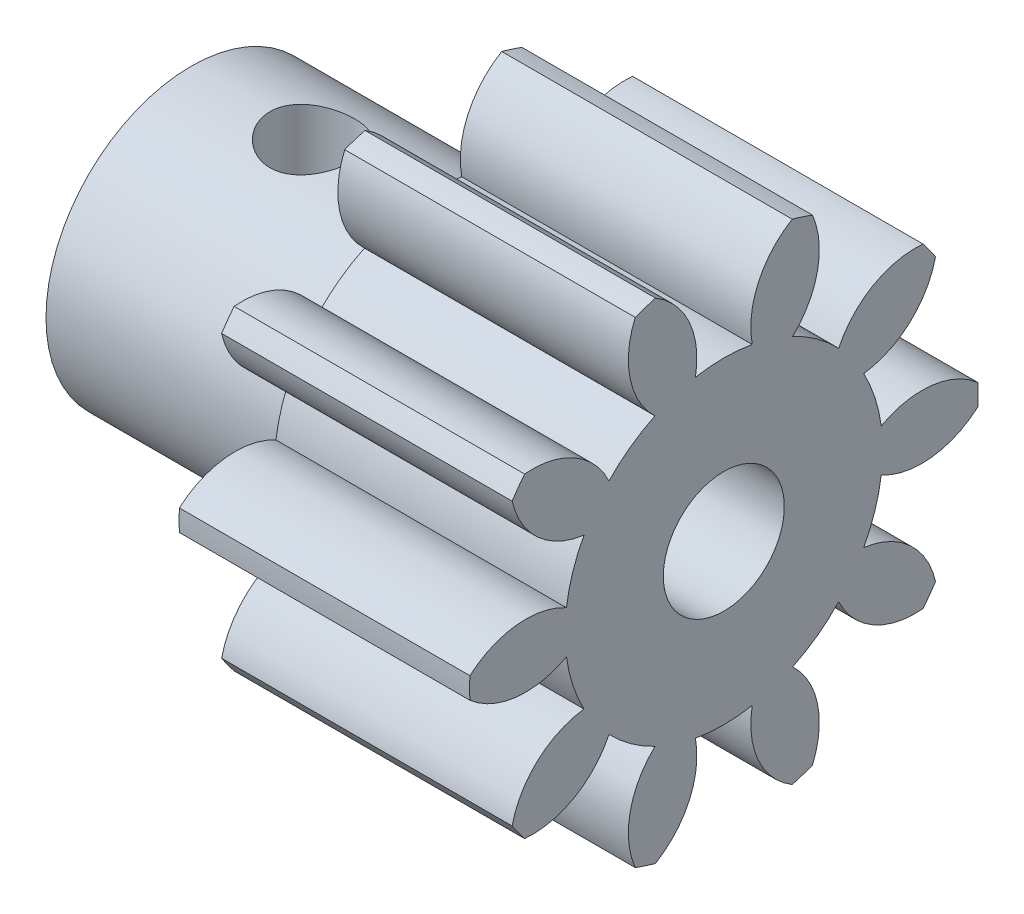
SolidWorks part; units mm, degrees
ref_plane "Plane1" through (0, 0, 0) normal (0, 0, 1) x (1, 0, 0)
ref_plane "Plane2" through (0, 0, 0) normal (0, 1, 0) x (1, 0, 0)
ref_plane "Plane3" through (0, 0, 0) normal (1, 0, 0) x (0, 0, -1)
sketch "HoldingSke" plane through (0, 0, 0) normal (0, 1, 0) x (1, 0, 0)
  line L0 (0, 0) -> (0.5627, -0.0992)
  line L1 (-15, 0) -> (100, 0) construction
  line L2 (0, 0) -> (-2.1039, 2.3779)
  line L3 (0, 0) -> (-11.863, 4.5341)
  line L4 (0, 0) -> (8.5048, 1.4996)
  line L5 (0, 0) -> (-46.8476, -17.4728)
  line L6 (0, 0) -> (-9.9476, -6.7116)
  line L7 (-2.1039, 2.3779) -> (8.6586, 51.2059)
  line L8 (-76.2, 54.61) -> (-75.3, 54.61)
  line L9 (-67.7845, 28.3722) -> (-49.3413, 33.142)
  line L10 (-76.2, 71.12) -> (104.1128, 71.12)
  line L11 (0, 0) -> (-12, 0)
  line L12 (-76.2, 101.6) -> (-76.147, 101.6)
  line L13 (24.9733, 27.94) -> (52.9518, 28.4284)
  line L14 (24.9733, 27.94) -> (24.9743, 27.94)
  line L15 (24.9733, 27.94) -> (100.4006, 29.5858)
  line L16 (-63.627, -1.75) -> (-12.827, -1.75)
  circle A0 centre (0, 0) radius 2.5
  circle A1 centre (0, 0) radius 6.5615
  circle A2 centre (0, 0) radius 37.5
  circle A3 centre (0, 0) radius 2.5
  dimension "MHD" = 13.123
  dimension "Hub_dia" = 75
  dimension "Bore" = 5
  dimension "MBD" = 5
  dimension "Num_teeth" = 10
  dimension "Pitch" = 0.5714
  dimension "Overall_len" = 50
  dimension "Show_teeth" = 10
  dimension "Thickness" = 12
  dimension "OAL" = 50.0001
  dimension "T_dim" = 0.9
  dimension "Ap" = 14.5
  dimension "H" = 19.05
  dimension "Pitch_radius" = 180.3128
  dimension "Width" = 12
  dimension "Backlash" = 0.053
  dimension "Addendum_fac" = 1
  dimension "Dedendum_fac" = 1.25
  dimension "Clearance_fac" = 0.25
  dimension "Dedendum_add" = 0.001
  dimension "Module" = 1.75
sketch "BasProSke" plane through (0, 0, 0) normal (0, 1, 0) x (1, 0, 0)
  line L0 (-10, 0) -> (60, 0) construction
  line L1 (0, 0) -> (0, 10.5)
  line L2 (0, 0) -> (12, 0)
  line L3 (12, 0) -> (12, 10.5)
  line L4 (12, 10.5) -> (0, 10.5)
  dimension "Thickness" = 12
  dimension "Diameter" = 21
revolve "Base-Revolve" add sketch "BasProSke" angle 360 about L0
sketch "TooCutSke" plane through (0, 0, 0) normal (1, 0, 0) x (0, 0, -1)
  line L1 (0, 0) -> (0, 107) construction
  line L2 (0, 0) -> (-1.4614, 8.6271) construction
  line L3 (0, 0) -> (-5.35, 16.4656) construction
  line L4 (-1.4614, 8.6271) -> (-2.675, 8.2328) construction
  arc A0 (1.1739, 6.4556) -> (-1.1739, 6.4556) centre (0, 0) ccw
  arc A1 (2.8542, 10.131) -> (-2.8542, 10.131) centre (0, 0) ccw
  circle A2 centre (0, 0) radius 8.75 construction
  circle A3 centre (0, 0) radius 8.4713 construction
  arc A4 (-1.1739, 6.4556) -> (-2.8542, 10.131) centre (-4.6131, 7.1051) ccw
  arc A5 (2.8542, 10.131) -> (1.1739, 6.4556) centre (4.6131, 7.1051) ccw
  dimension "Root_dia" = 13.123
  dimension "Overcut_dia" = 21.0508
  dimension "Pitch_dia" = 17.5
  dimension "Base_dia" = 16.9426
  dimension "Flank_rad" = 3.5
  dimension "Half_ang" = 18
  dimension "Half_CT" = 1.2761
extrude "ToothCut" cut sketch "TooCutSke" along normal through all
fillet "Breaks" [suppressed] radius 0.035
fillet "RootFillets" [suppressed] radius 0.4385
pattern_circular "TeethCuts" count 10 every 36 about axis through (-10, 0, 0) along (1, 0, 0) of "ToothCut"
sketch "HubNeaOneSke" plane through (0, 0, 0) normal (-1, 0, 0) x (0, 0, 1)
  circle A0 centre (0, 0) radius 6.5615
  dimension "Diameter" = 13.123
extrude "HubNearOne" [suppressed] add sketch "HubNeaOneSke" along normal blind 38.0001
sketch "HubNeaBotSke" plane through (0, 0, 0) normal (-1, 0, 0) x (0, 0, 1)
  circle A0 centre (0, 0) radius 6.5615
  dimension "Diameter" = 13.123
extrude "HubNearBoth" [suppressed] add sketch "HubNeaBotSke" along normal blind 19
ref_plane "FarPln" through (12, 0, 0) normal (1, 0, 0) x (0, 0, -1)
sketch "HubFarSke" plane through (12, 0, 0) normal (1, 0, 0) x (0, 0, -1)
  circle A0 centre (0, 0) radius 6.5615
  dimension "Diameter" = 13.123
extrude "HubFar" [suppressed] add sketch "HubFarSke" along normal blind 19
sketch "BorSke" plane through (0, 0, 0) normal (1, 0, 0) x (0, 0, -1)
  circle A0 centre (0, 0) radius 2.5
  dimension "Diameter" = 5
extrude "Bore" cut sketch "BorSke" along normal mid plane 100.0001
sketch "KeySke" plane through (0, 0, 0) normal (1, 0, 0) x (0, 0, -1)
  line L0 (-1, 0) -> (-1, 3.4)
  line L1 (-1, 3.4) -> (1, 3.4)
  line L2 (1, 3.4) -> (1, 0)
  line L3 (0, 0) -> (0, 34) construction
  line L4 (-1, 0) -> (1, 0)
  dimension "Offset" = 3.4
  dimension "Width" = 2
extrude "Keyway" [suppressed] cut sketch "KeySke" along normal mid plane 100.0001
pattern_circular "Keyway2" [suppressed] count 2 every 90 about axis through (-10, 0, 0) along (1, 0, 0)
sketch "Sketch2" plane through (0, 0, 0) normal (-1, 0, 0) x (0, 0, 1)
  line L0 (0, 2.75) -> (0, 2.25)
  line L1 (-1.5811, 2.25) -> (1.5811, 2.25)
  circle A0 centre (0, 0) radius 2.75
  circle A1 centre (0, 0) radius 6
  point P12 (0, 2.25)
  circle M2 centre (0, 0) radius 2.5
extrude "Boss-Extrude1" add sketch "Sketch2" along normal blind 10 contours A1 A0 | L1 A0 L0 M2 | L0 A0 L1 M2 | L0 L1 M2 | L1 L0 M2
sketch "Sketch4" plane through (0, 0, 0) normal (0, 1, 0) x (1, 0, 0)
  line L0 (-10, 0) -> (0, 0)
  line L1 (-10, 6) -> (-10, -6) construction
  line L2 (0, 1.1739) -> (0, -1.1739) construction
  circle A0 centre (-5, 0) radius 1.75
extrude "Cut-Extrude1" cut sketch "Sketch4" along normal blind 10 contours L0 A0 | L0 A0
equation "' \"Module@HoldingSke\" = 6.35"
equation "' \"Num_teeth@HoldingSke\" = 12"
equation "' \"Ap@HoldingSke\" =  20"
equation "' \"Ap@HoldingSke\" = 20"
equation "' \"Width@HoldingSke\" = 0.5 * 25.4"
equation "' \"Hub_dia@HoldingSke\"= 1 * 25.4"
equation "' \"Hub_dia@HoldingSke\" = 1 * 25.4"
equation "' \"Overall_len@HoldingSke\" = 1.0 * 25.4"
equation "' \"Bore@HoldingSke\" = 0.75 * 25.4"
equation "' \"T_dim@HoldingSke\" = 0.1 * 25.4"
equation "' \"Width@KeySke\" = 0.25 * 25.4"
equation "' \"Show_teeth@HoldingSke\" = 13"
equation "' \"Backlash@HoldingSke\" = 0.009 * 25.4"
equation "' \"Addendum_fac@HoldingSke\" = 1.0"
equation "' \"Dedendum_fac@HoldingSke\" = 1.25"
equation "' \"Dedendum_add@HoldingSke\" = 0.00005 * 25.4"
equation "' \"Clearance_fac@HoldingSke\" = 0.25"
equation "\"Pitch@HoldingSke\" = 1 / \"Module@HoldingSke\""
equation "\"Overcut_dia@TooCutSke\" = (\"Num_teeth@HoldingSke\" + 2 * \"Addendum_fac@HoldingSke\") / \"Pitch@HoldingSke\" + 0.002 * 25.4"
equation "\"Pitch_dia@TooCutSke\" = \"Num_teeth@HoldingSke\" / \"Pitch@HoldingSke\""
equation "\"Base_dia@TooCutSke\" = \"Num_teeth@HoldingSke\" / \"Pitch@HoldingSke\" * cos((\"Ap@HoldingSke\"  * 3.14159265 / 180))"
equation "\"Root_dia@TooCutSke\" = (\"Num_teeth@HoldingSke\" + 2) / \"Pitch@HoldingSke\" - 2 * (\"Addendum_fac@HoldingSke\" + \"Dedendum_fac@HoldingSke\") / \"Pitch@HoldingSke\" - \"Dedendum_add@HoldingSke\" * 2"
equation "\"Half_ang@TooCutSke\" = 180 / \"Num_teeth@HoldingSke\""
equation "\"Half_CT@TooCutSke\" = \"Num_teeth@HoldingSke\" / \"Pitch@HoldingSke\" * sin((3.14159265 / 2 / \"Num_teeth@HoldingSke\")) / 2 - 7 * \"Backlash@HoldingSke\" / 4"
equation "\"Flank_rad@TooCutSke\" = \"Num_teeth@HoldingSke\" / \"Pitch@HoldingSke\" / 5"
equation "\"Radius@RootFillets\" = \"Clearance_fac@HoldingSke\" / \"Pitch@HoldingSke\" + \"Dedendum_add@HoldingSke\""
equation "\"Break_rad@Breaks\" = 0.02 / \"Pitch@HoldingSke\""
equation "\"Thickness@HoldingSke\" = \"Width@HoldingSke\""
equation "\"OAL@HoldingSke\" = \"Thickness@HoldingSke\""
equation "\"MHD@HoldingSke\" = (\"Num_teeth@HoldingSke\" + 2) / \"Pitch@HoldingSke\" - 2 * (\"Addendum_fac@HoldingSke\" + \"Dedendum_fac@HoldingSke\")  / \"Pitch@HoldingSke\" - \"Dedendum_add@HoldingSke\" * 2"
equation "\"MBD@HoldingSke\" = (\"Num_teeth@HoldingSke\" + 2) / \"Pitch@HoldingSke\" - 2 * (\"Addendum_fac@HoldingSke\" + \"Dedendum_fac@HoldingSke\")  / \"Pitch@HoldingSke\" - \"Dedendum_add@HoldingSke\" * 2 - 0.002 * 25.4"
equation "\"MHD@HoldingSke\" = ((sgn( \"MHD@HoldingSke\" - \"Hub_dia@HoldingSke\" )-1)*( \"MHD@HoldingSke\" - \"Hub_dia@HoldingSke\" ))/-2+ \"Hub_dia@HoldingSke\""
equation "\"MBD@HoldingSke\" = ((sgn( \"MBD@HoldingSke\" - \"Bore@HoldingSke\" )-1)*( \"MBD@HoldingSke\" - \"Bore@HoldingSke\" ))/-2+ \"Bore@HoldingSke\""
equation "\"OAL@HoldingSke\" = ((sgn( \"OAL@HoldingSke\" - \"Overall_len@HoldingSke\" )+1)*( \"OAL@HoldingSke\" - \"Overall_len@HoldingSke\" ))/2 + \"Overall_len@HoldingSke\" + 0.000002 * 25.4"
equation "\"Num_teeth@TeethCuts\" = int( \"Show_teeth@HoldingSke\" ) + 1"
equation "\"Num_teeth@TeethCuts\" = ((sgn( \"Num_teeth@TeethCuts\" - \"Num_teeth@HoldingSke\" )-1)*( \"Num_teeth@TeethCuts\" - \"Num_teeth@HoldingSke\" ))/-2+ \"Num_teeth@HoldingSke\""
equation "\"Num_teeth@TeethCuts\" = ((sgn( \"Num_teeth@TeethCuts\" - 2.0)+1)*( \"Num_teeth@TeethCuts\" - 2.0))/2 +2.0"
equation "\"Angle@TeethCuts\" = 360.0 / \"Num_teeth@HoldingSke\""
equation "\"Diameter@BasProSke\" = (\"Num_teeth@HoldingSke\" + 2 * \"Addendum_fac@HoldingSke\") / \"Pitch@HoldingSke\""
equation "\"Thickness@BasProSke\"  = \"Thickness@HoldingSke\""
equation "' \"Fillet_rad@BasProSke\" =  \"Thickness@HoldingSke\" * 0.05"
equation "' \"Fillet_rad@BasProSke\" = \"Thickness@HoldingSke\" * 0.05"
equation "\"MHD@HoldingSke\" = ((sgn( \"MHD@HoldingSke\" - \"Root_dia@TooCutSke\" )-1)*( \"MHD@HoldingSke\" - \"Root_dia@TooCutSke\" ))/-2+ \"Root_dia@TooCutSke\""
equation "\"Diameter@HubNeaOneSke\" = \"MHD@HoldingSke\""
equation "\"Length@HubNearOne\" = \"OAL@HoldingSke\" - \"Thickness@BasProSke\""
equation "\"Diameter@HubNeaBotSke\" = \"MHD@HoldingSke\""
equation "\"Length@HubNearBoth\" = ( \"OAL@HoldingSke\" - \"Thickness@BasProSke\" ) / 2.0"
equation "\"Thickness@FarPln\" = \"Thickness@BasProSke\""
equation "\"Diameter@HubFarSke\" = \"MHD@HoldingSke\""
equation "\"Length@HubFar\" = ( \"OAL@HoldingSke\" - \"Thickness@BasProSke\" ) / 2.0"
equation "\"Diameter@BorSke\" = \"MBD@HoldingSke\""
equation "\"D1@Bore\" = \"OAL@HoldingSke\" * 2.0"
equation "\"D1@Keyway\" = \"OAL@HoldingSke\" * 2.0"
equation "\"Offset@KeySke\" = \"T_dim@HoldingSke\" + \"MBD@HoldingSke\" / 2.0"
